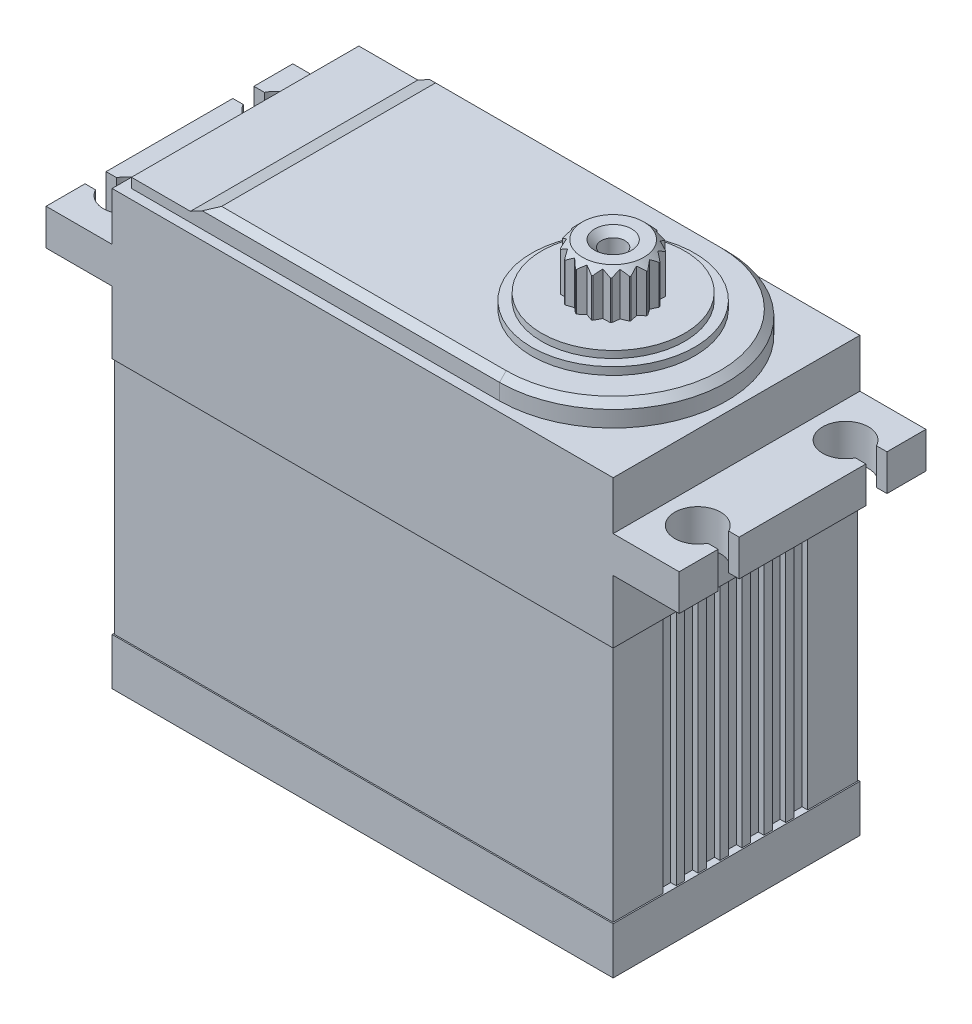
SolidWorks part; units mm, degrees
ref_plane "Alzado" through (0, 0, 0) normal (0, 0, 1) x (1, 0, 0)
ref_plane "Planta" through (0, 0, 0) normal (0, 1, 0) x (1, 0, 0)
ref_plane "Vista lateral" through (0, 0, 0) normal (1, 0, 0) x (0, 0, -1)
sketch "Croquis1" plane through (0, 0, 0) normal (0, 0, 1) x (1, 0, 0)
  line L0 (0, 0) -> (59.5, 0)
  line L1 (59.5, 0) -> (59.5, 5.58)
  line L2 (59.5, 5.58) -> (59.355, 5.58)
  line L3 (59.355, 5.58) -> (59.355, 33.93)
  line L4 (59.355, 33.93) -> (59.5, 33.93)
  line L5 (59.5, 33.93) -> (59.5, 41.4)
  line L6 (59.5, 41.4) -> (67.34, 41.4)
  line L7 (67.34, 41.4) -> (67.34, 45.7)
  line L8 (67.34, 45.7) -> (59.5, 45.7)
  line L9 (59.5, 45.7) -> (59.5, 51.45)
  line L10 (59.5, 51.45) -> (0, 51.45)
  line L11 (0, 51.45) -> (0, 45.7)
  line L12 (0, 45.7) -> (-7.84, 45.7)
  line L13 (-7.84, 45.7) -> (-7.84, 41.4)
  line L14 (-7.84, 41.4) -> (0, 41.4)
  line L15 (0, 41.4) -> (0, 33.93)
  line L16 (0, 33.93) -> (0.145, 33.93)
  line L17 (0.145, 33.93) -> (0.145, 5.58)
  line L18 (0.145, 5.58) -> (0, 5.58)
  line L19 (0, 5.58) -> (0, 0)
  line L20 (29.75, 13.0616) -> (29.75, 65.692) construction
  dimension "D1" = 59.5
  dimension "D2" = 59.21
  dimension "D3" = 75.18
  dimension "D4" = 51.45
  dimension "D5" = 4.3
  dimension "D6" = 45.7
  dimension "D7" = 28.35
  dimension "D8" = 5.58
extrude "Saliente-Extruir1" add sketch "Croquis1" along normal blind 29.3
sketch "Croquis2" plane through (0, 5.58, 0) normal (0, 1, 0) x (1, 0, 0)
  line L0 (0.155, -0.15) -> (59.345, -0.15)
  line L1 (59.345, -0.15) -> (59.345, -6.05)
  line L2 (-11.8648, 8.0152) -> (73.3465, 8.0152)
  line L3 (-11.8648, 8.0152) -> (-11.8648, -42.1455)
  line L4 (-11.8648, -42.1455) -> (73.3465, -42.1455)
  line L5 (73.3465, 8.0152) -> (73.3465, -42.1455)
  line L6 (59.345, -6.05) -> (58.685, -6.05)
  line L7 (58.685, -6.05) -> (58.685, -7.65)
  line L8 (58.685, -7.65) -> (59.345, -7.65)
  line L9 (59.345, -7.65) -> (59.345, -8.65)
  line L10 (59.345, -8.65) -> (58.685, -8.65)
  line L11 (58.685, -8.65) -> (58.685, -10.25)
  line L12 (58.685, -10.25) -> (59.345, -10.25)
  line L13 (59.345, -10.25) -> (59.345, -11.25)
  line L14 (59.345, -11.25) -> (58.685, -11.25)
  line L15 (58.685, -11.25) -> (58.685, -12.85)
  line L16 (58.685, -12.85) -> (59.345, -12.85)
  line L17 (59.345, -12.85) -> (59.345, -13.85)
  line L18 (59.345, -13.85) -> (58.685, -13.85)
  line L19 (58.685, -13.85) -> (58.685, -15.45)
  line L20 (58.685, -15.45) -> (59.345, -15.45)
  line L21 (59.345, -15.45) -> (59.345, -16.45)
  line L22 (59.345, -16.45) -> (58.685, -16.45)
  line L23 (58.685, -16.45) -> (58.685, -18.05)
  line L24 (58.685, -18.05) -> (59.345, -18.05)
  line L25 (59.345, -18.05) -> (59.345, -19.05)
  line L26 (59.345, -19.05) -> (58.685, -19.05)
  line L27 (58.685, -19.05) -> (58.685, -20.65)
  line L28 (58.685, -20.65) -> (59.345, -20.65)
  line L29 (59.345, -20.65) -> (59.345, -21.65)
  line L30 (59.345, -21.65) -> (58.685, -21.65)
  line L31 (58.685, -21.65) -> (58.685, -23.25)
  line L32 (58.685, -23.25) -> (59.345, -23.25)
  line L33 (59.345, -23.25) -> (59.345, -29.15)
  line L34 (59.345, -29.15) -> (0.155, -29.15)
  line L35 (59.5, 0) -> (0, 0) construction
  line L37 (59.5, -29.3) -> (0, -29.3) construction
  line L38 (29.75, 13.1082) -> (29.75, -55.8837) construction
  line L39 (-7.84, -29.3) -> (-7.84, 0) construction
  line L40 (67.34, -29.3) -> (67.34, 0) construction
  line L41 (0.155, -23.25) -> (0.155, -29.15)
  line L42 (0.815, -23.25) -> (0.155, -23.25)
  line L43 (0.815, -21.65) -> (0.815, -23.25)
  line L44 (0.155, -21.65) -> (0.815, -21.65)
  line L45 (0.155, -20.65) -> (0.155, -21.65)
  line L46 (0.815, -20.65) -> (0.155, -20.65)
  line L47 (0.815, -19.05) -> (0.815, -20.65)
  line L48 (0.155, -19.05) -> (0.815, -19.05)
  line L49 (0.155, -18.05) -> (0.155, -19.05)
  line L50 (0.815, -18.05) -> (0.155, -18.05)
  line L51 (0.815, -16.45) -> (0.815, -18.05)
  line L52 (0.155, -16.45) -> (0.815, -16.45)
  line L53 (0.155, -15.45) -> (0.155, -16.45)
  line L54 (0.815, -15.45) -> (0.155, -15.45)
  line L55 (0.815, -13.85) -> (0.815, -15.45)
  line L56 (0.155, -13.85) -> (0.815, -13.85)
  line L57 (0.155, -12.85) -> (0.155, -13.85)
  line L58 (0.815, -12.85) -> (0.155, -12.85)
  line L59 (0.815, -11.25) -> (0.815, -12.85)
  line L60 (0.155, -11.25) -> (0.815, -11.25)
  line L61 (0.155, -10.25) -> (0.155, -11.25)
  line L62 (0.815, -10.25) -> (0.155, -10.25)
  line L63 (0.815, -8.65) -> (0.815, -10.25)
  line L64 (0.155, -8.65) -> (0.815, -8.65)
  line L65 (0.155, -7.65) -> (0.155, -8.65)
  line L66 (0.815, -7.65) -> (0.155, -7.65)
  line L67 (0.815, -6.05) -> (0.815, -7.65)
  line L68 (0.155, -6.05) -> (0.815, -6.05)
  line L69 (59.355, -29.3) -> (59.355, 0) construction
  line L70 (0.155, -0.15) -> (0.155, -6.05)
  line L73 (0.145, -29.3) -> (0.145, 0) construction
  dimension "D1" = 0.15
  dimension "D2" = 5.9
  dimension "D3" = 1.6
  dimension "D4" = 1.6
  dimension "D5" = 1.6
  dimension "D6" = 1.6
  dimension "D7" = 1.6
  dimension "D8" = 1.6
  dimension "D9" = 1.6
  dimension "D10" = 1
  dimension "D11" = 1
  dimension "D12" = 1
  dimension "D13" = 1
  dimension "D14" = 1
  dimension "D15" = 1
  dimension "D16" = 0.15
  dimension "D17" = 0.66
  dimension "D18" = 0.01
  dimension "D19" = 0.01
extrude "Cortar-Extruir1" cut sketch "Croquis2" along normal up to surface (28.35 mm away) up to face at (0.0725, 33.93, 14.65)
sketch "Croquis3" plane through (0, 45.7, 0) normal (0, 1, 0) x (1, 0, 0)
  line L0 (-14.1617, -3.15) -> (-1.45, -3.15) construction
  line L1 (-1.45, -3.15) -> (-1.45, -11.4958) construction
  line L2 (0, 0) -> (-7.84, 0) construction
  line L3 (0, -29.3) -> (0, 0) construction
  line L4 (-2.6117, -5.875) -> (-5.0339, -5.875) construction
  line L5 (-8.6281, -4.625) -> (-6.5964, -4.625)
  line L6 (-8.6281, -4.625) -> (-8.6281, -7.125)
  line L7 (-8.6281, -7.125) -> (-6.5964, -7.125)
  line L8 (29.75, 7.7601) -> (29.75, -14.65) construction
  line L9 (29.75, -14.65) -> (8.494, -14.65) construction
  line L10 (59.5, 0) -> (0, 0) construction
  line L11 (59.5, -29.3) -> (0, -29.3) construction
  line L12 (-7.84, -29.3) -> (-7.84, 0) construction
  line L13 (67.34, -29.3) -> (67.34, 0) construction
  line L14 (62.1117, -5.875) -> (64.5339, -5.875) construction
  line L15 (60.95, -3.15) -> (60.95, -11.4958) construction
  line L16 (73.6617, -3.15) -> (60.95, -3.15) construction
  line L17 (68.1281, -7.125) -> (66.0964, -7.125)
  line L18 (68.1281, -4.625) -> (68.1281, -7.125)
  line L19 (68.1281, -4.625) -> (66.0964, -4.625)
  line L20 (73.6617, -26.15) -> (60.95, -26.15) construction
  line L21 (60.95, -26.15) -> (60.95, -17.8042) construction
  line L22 (62.1117, -23.425) -> (64.5339, -23.425) construction
  line L23 (68.1281, -24.675) -> (66.0964, -24.675)
  line L24 (68.1281, -24.675) -> (68.1281, -22.175)
  line L25 (68.1281, -22.175) -> (66.0964, -22.175)
  line L26 (-2.6117, -23.425) -> (-5.0339, -23.425) construction
  line L27 (-1.45, -26.15) -> (-1.45, -17.8042) construction
  line L28 (-14.1617, -26.15) -> (-1.45, -26.15) construction
  line L29 (-8.6281, -22.175) -> (-6.5964, -22.175)
  line L30 (-8.6281, -24.675) -> (-8.6281, -22.175)
  line L31 (-8.6281, -24.675) -> (-6.5964, -24.675)
  arc A0 (-6.5964, -7.125) -> (-6.5964, -4.625) centre (-4.175, -5.875) ccw
  arc A1 (66.0964, -7.125) -> (66.0964, -4.625) centre (63.675, -5.875) cw
  arc A2 (66.0964, -22.175) -> (66.0964, -24.675) centre (63.675, -23.425) ccw
  arc A3 (-6.5964, -22.175) -> (-6.5964, -24.675) centre (-4.175, -23.425) cw
  dimension "D3" = 5.45
  dimension "D1" = 3.15
  dimension "D2" = 1.45
  dimension "D4" = 2.5
extrude "Cortar-Extruir2" cut sketch "Croquis3" against normal up to next
sketch "Croquis4" plane through (0, 51.45, 0) normal (0, 1, 0) x (1, 0, 0)
  line L0 (0, -29.3) -> (0, 0) construction
  line L1 (1.15, -1.15) -> (44.85, -1.15)
  line L2 (1.15, -1.15) -> (1.15, -28.15)
  line L3 (1.15, -28.15) -> (44.85, -28.15)
  line L4 (58.35, -0.8) -> (58.35, -32.9652) construction
  line L5 (59.5, 0) -> (0, 0) construction
  line L6 (59.5, -29.3) -> (0, -29.3) construction
  line L7 (59.5, -29.3) -> (59.5, 0) construction
  arc A0 (44.85, -28.15) -> (44.85, -1.15) centre (44.85, -14.65) ccw
  dimension "D1" = 1.15
  dimension "D2" = 1.15
  dimension "D3" = 1.15
  dimension "D4" = 1.15
extrude "Saliente-Extruir2" add sketch "Croquis4" along normal blind 1.15
sketch "Croquis5" plane through (0, 52.6, 0) normal (0, 1, 0) x (1, 0, 0)
  line L0 (8.15, -1.15) -> (44.85, -1.15)
  line L1 (8.15, -1.15) -> (8.15, -28.15)
  line L2 (8.15, -28.15) -> (44.85, -28.15)
  line L3 (58.35, 6.7884) -> (58.35, -25.3768) construction
  line L4 (44.85, -1.15) -> (1.15, -1.15) construction
  line L5 (1.15, -28.15) -> (44.85, -28.15) construction
  line L6 (1.15, -1.15) -> (1.15, -28.15) construction
  arc A0 (44.85, -28.15) -> (44.85, -1.15) centre (44.85, -14.65) ccw
  arc A1 (44.85, -28.15) -> (44.85, -1.15) centre (44.85, -14.65) ccw construction
  dimension "D1" = 7
extrude "Saliente-Extruir3" add sketch "Croquis5" along normal blind 1.56
chamfer "Chaflán1" distance 0.8 angle 45 4 edges at (26.5, 54.16, 1.15) (58.35, 54.16, 14.65) (26.5, 54.16, 28.15) (8.15, 54.16, 14.65)
sketch "Croquis6" plane through (0, 0, 29.3) normal (0, 0, 1) x (1, 0, 0)
  line L0 (-14.4185, 52.6) -> (8.15, 52.6)
  line L1 (8.15, 52.6) -> (21.571, 59.8076)
  line L2 (21.571, 59.8076) -> (-14.4185, 52.6)
  line L3 (1.15, 52.6) -> (8.15, 52.6) construction
extrude "Cortar-Extruir3" cut sketch "Croquis6" against normal through all
sketch "Croquis7" plane through (0, 54.16, 0) normal (0, 1, 0) x (1, 0, 0)
  line L0 (33.2943, -4.97) -> (60.7712, -4.97) construction
  circle A0 centre (44.85, -14.65) radius 9.68
  arc A1 (44.85, -27.35) -> (44.85, -1.95) centre (44.85, -14.65) ccw construction
  dimension "D1" = 19.36
extrude "Saliente-Extruir4" add sketch "Croquis7" along normal blind 0.9
sketch "Croquis8" plane through (0, 55.06, 0) normal (0, 1, 0) x (1, 0, 0)
  circle A0 centre (44.85, -14.65) radius 8.49
  dimension "D1" = 16.98
extrude "Saliente-Extruir5" add sketch "Croquis8" along normal blind 0.83
sketch "Croquis9" plane through (0, 55.89, 0) normal (0, 1, 0) x (1, 0, 0)
  circle A0 centre (44.85, -14.65) radius 4.445
  circle A1 centre (44.85, -14.65) radius 8.49 construction
  circle A2 centre (44.85, -14.65) radius 1.4
  dimension "D1" = 8.89
  dimension "D2" = 2.8
extrude "Saliente-Extruir6" add sketch "Croquis9" along normal blind 5.4
chamfer "Chaflán2" distance 0.8 angle 45 2 edges at (44.85, 61.29, 19.095) (44.85, 61.29, 16.05)
sketch "Croquis10" plane through (0, 61.29, 0) normal (0, 1, 0) x (1, 0, 0)
  line L0 (37.4542, -6.4561) -> (44.8135, -10.705)
  line L1 (44.8135, -10.705) -> (52.1729, -6.4561)
  line L2 (52.1729, -6.4561) -> (37.4542, -6.4561)
  line L3 (41.244, -10.205) -> (48.2691, -10.205) construction
  line L4 (44.8135, -10.705) -> (44.8135, -9.3557) construction
  circle A0 centre (44.85, -14.65) radius 4.445 construction
  dimension "D1" = 0.5
  dimension "D2" = 120
  dimension "D3" = 60
extrude "Cortar-Extruir4" cut sketch "Croquis10" against normal up to surface (5.4 mm away) up to face at (44.85, 55.89, 23.14)
pattern_circular "MatrizC1" count 17 over 360 about axis through (44.85, 0, 14.65) along (0, 1, 0) of "Cortar-Extruir4"
